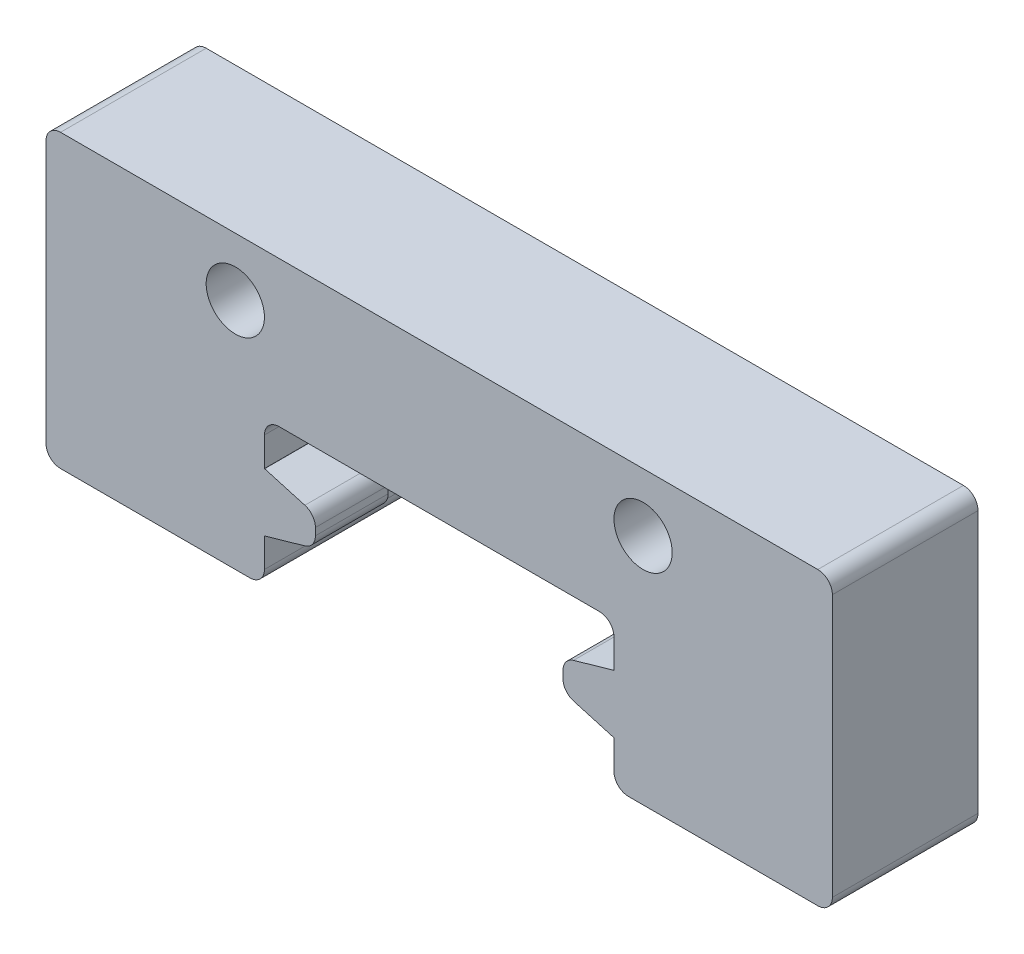
SolidWorks part; units mm, degrees
ref_plane "Front Plane" through (0, 0, 0) normal (0, 0, 1) x (1, 0, 0)
ref_plane "Top Plane" through (0, 0, 0) normal (0, 1, 0) x (1, 0, 0)
ref_plane "Right Plane" through (0, 0, 0) normal (1, 0, 0) x (0, 0, -1)
sketch "Sketch1" plane through (0, 0, 0) normal (0, 0, 1) x (1, 0, 0)
  line L0 (-6, -1.5) -> (-6, 0)
  line L1 (-13.5, 5) -> (13.5, 5)
  line L2 (-13.5, 5) -> (-13.5, -5)
  line L3 (-13.5, -5) -> (-6, -5)
  line L4 (13.5, 5) -> (13.5, -5)
  line L5 (-13.5, 5) -> (13.5, -5) construction
  line L6 (-13.5, -5) -> (13.5, 5) construction
  line L8 (-6, -5) -> (-6, -3.5)
  line L9 (-6, 0) -> (6, 0)
  line L10 (6, -5) -> (6, -3.5)
  line L11 (-6, -1.5) -> (-4.25, -1.5)
  line L13 (-6, -3.5) -> (-4.25, -3.5)
  line L14 (-4.25, -1.5) -> (-4.25, -3.5)
  line L15 (6, -1.5) -> (4.25, -1.5)
  line L17 (6, -3.5) -> (4.25, -3.5)
  line L18 (4.25, -1.5) -> (4.25, -3.5)
  line L19 (6, -1.5) -> (6, 0)
  line L20 (6, -5) -> (13.5, -5)
  point P0 (0, 0)
  dimension "D1" = 27
  dimension "D2" = 10
  dimension "D3" = 12
  dimension "D4" = 6
  dimension "D5" = 5
  dimension "D6" = 8.5
  dimension "D7" = 4.25
  dimension "D8" = 2
  dimension "D9" = 2
  dimension "D10" = 1.5
  dimension "D11" = 1.5
extrude "Boss-Extrude1" add sketch "Sketch1" along normal blind 5
chamfer "Chamfer1" distance 0.5 angle 74 4 edges at (4.25, -3.5, 2.5) (4.25, -1.5, 2.5) (-4.25, -3.5, 2.5) (-4.25, -1.5, 2.5)
fillet "Fillet1" radius 0.5 4 edges at (-4.25, -3, 2.5) (-4.25, -2, 2.5) (4.25, -3, 2.5) (4.25, -2, 2.5)
sketch "Sketch2" plane through (0, 0, 5) normal (0, 0, 1) x (1, 0, 0)
  line L0 (13.5, 5) -> (-13.5, 5) construction
  circle A0 centre (-7, 3) radius 1
  circle A1 centre (7, 3) radius 1
  dimension "D3" = 2
  dimension "D4" = 2
  dimension "D1" = 14
  dimension "D2" = 7
  dimension "D5" = 2
  dimension "D6" = 2
extrude "Cut-Extrude1" cut sketch "Sketch2" against normal blind 5
fillet "Fillet2" radius 0.5 8 edges at (13.5, 5, 2.5) (13.5, -5, 2.5) (6, -5, 2.5) (6, 0, 2.5) (-6, 0, 2.5) (-6, -5, 2.5) (-13.5, -5, 2.5) (-13.5, 5, 2.5)
sketch "Sketch4" plane through (0, 0, 0) normal (0, 0, -1) x (-1, 0, 0)
  line L0 (5.5, 0) -> (-5.5, 0) construction
  line L1 (-11, -1.25) -> (-4.25, -1.25)
  line L2 (-11, -1.25) -> (-11, -3.75)
  line L3 (-11, -3.75) -> (-4.25, -3.75)
  line L4 (-4.25, -1.25) -> (-4.25, -3.75)
  line L5 (11, -1.25) -> (4.25, -1.25)
  line L6 (11, -1.25) -> (11, -3.75)
  line L7 (11, -3.75) -> (4.25, -3.75)
  line L8 (4.25, -1.25) -> (4.25, -3.75)
  dimension "D1" = 2.5
  dimension "D2" = 2.5
  dimension "D3" = 1.25
  dimension "D4" = 1.25
  dimension "D5" = 8.5
  dimension "D6" = 4.25
  dimension "D7" = 22
  dimension "D8" = 11
extrude "Cut-Extrude2" cut sketch "Sketch4" against normal blind 2.5
